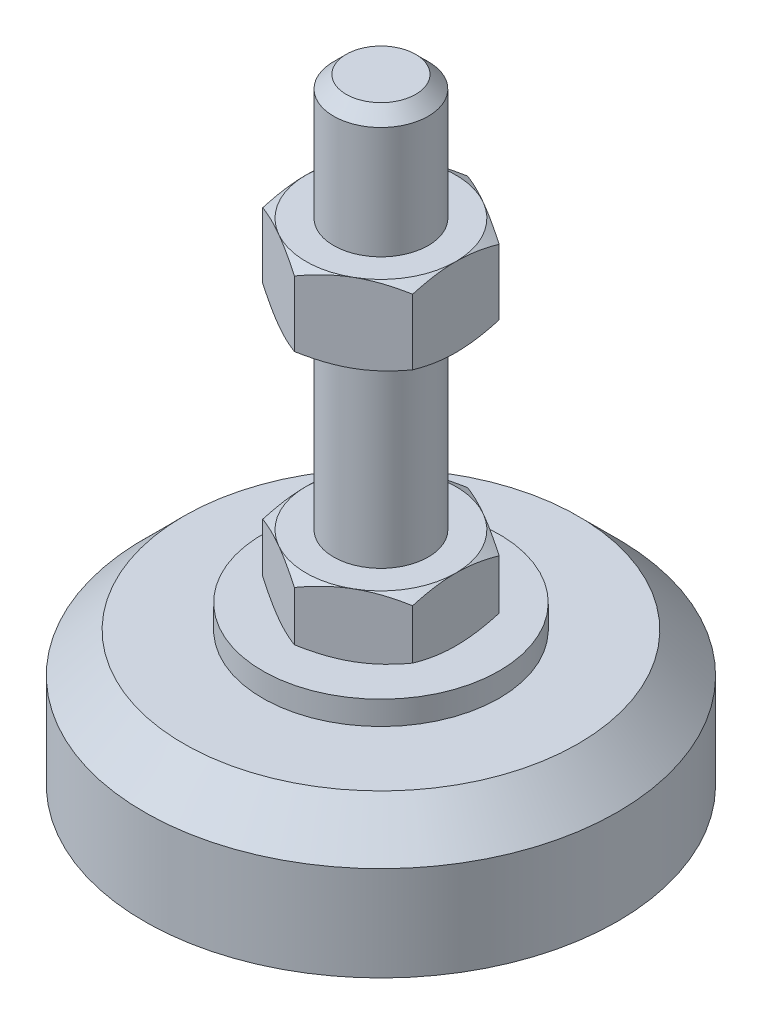
SolidWorks part; units mm, degrees
ref_plane "Спереди" through (0, 0, 0) normal (0, 0, 1) x (1, 0, 0)
ref_plane "Сверху" through (0, 0, 0) normal (0, 1, 0) x (1, 0, 0)
ref_plane "Справа" through (0, 0, 0) normal (1, 0, 0) x (0, 0, -1)
sketch "Эскиз1" plane through (0, 0, 0) normal (0, 0, 1) x (1, 0, 0)
  line L0 (0, 0) -> (-30, 0)
  line L3 (-30, 0) -> (-30, 12)
  line L5 (-15, 20) -> (-6, 20)
  line L12 (-6, 28) -> (-6, 76.4)
  line L13 (-6, 76.4) -> (-4.4, 78)
  line L14 (-4.4, 78) -> (0, 78)
  line L15 (0, 78) -> (0, 0) construction
  line L16 (-6, 20) -> (0, 20) construction
  line L17 (0, 0) -> (0, 78)
  line L18 (0, 0) -> (0, -7.9595) construction
  line L19 (-6, 28) -> (-6, 20)
  line L20 (-15, 20) -> (-15, 17)
  line L21 (-15, 17) -> (-25, 17)
  line L22 (-25, 17) -> (-30, 12)
  point P8 (-6, 52.2)
  point P23 (-10.5, 20)
  dimension "D1" = 12
  dimension "D2" = 20
  dimension "D3" = 8
  dimension "D4" = 60
  dimension "D5" = 6
  dimension "D6" = 1.6
  dimension "D7" = 45
  dimension "D8" = 30
  dimension "D10" = 50
  dimension "D11" = 12
  dimension "D12" = 45
  dimension "D13" = 3
revolve "Повернуть1" add sketch "Эскиз1" angle 360 about L17
sketch "Эскиз2" plane through (0, 20, 0) normal (0, 1, 0) x (1, 0, 0)
  line L1 (0, 10.9697) -> (-9.5, 5.4848)
  line L2 (-9.5, 5.4848) -> (-9.5, -5.4848)
  line L3 (-9.5, -5.4848) -> (0, -10.9697)
  line L4 (0, -10.9697) -> (9.5, -5.4848)
  line L5 (9.5, -5.4848) -> (9.5, 5.4848)
  line L6 (9.5, 5.4848) -> (0, 10.9697)
  circle A0 centre (0, 0) radius 9.5 construction
  dimension "D1" = 19
extrude "Бобышка-Вытянуть1" add sketch "Эскиз2" along normal up to vertex (8 mm away) up to point (-6, 28, 0)
ref_plane "Плоскость1" through (0, 52.2, 0) normal (0, 1, 0) x (1, 0, 0)
sketch "Эскиз3" plane through (0, 52.2, 0) normal (0, 1, 0) x (1, 0, 0)
  line L6 (9.5, 5.4848) -> (0, 10.9697)
  line L7 (0, 10.9697) -> (-9.5, 5.4848)
  line L8 (-9.5, 5.4848) -> (-9.5, -5.4848)
  line L9 (-9.5, -5.4848) -> (0, -10.9697)
  line L10 (0, -10.9697) -> (9.5, -5.4848)
  line L11 (9.5, -5.4848) -> (9.5, 5.4848)
  line L12 (9.5, 5.4848) -> (0, 10.9697)
  line L13 (0, 10.9697) -> (-9.5, 5.4848)
  line L14 (-9.5, 5.4848) -> (-9.5, -5.4848)
  line L15 (-9.5, -5.4848) -> (0, -10.9697)
  line L16 (0, -10.9697) -> (9.5, -5.4848)
  line L17 (9.5, -5.4848) -> (9.5, 5.4848)
  dimension "D1" = 0
extrude "Бобышка-Вытянуть2" add sketch "Эскиз3" along normal blind 10
sketch "Эскиз4" plane through (0, 0, 0) normal (0, 0, 1) x (1, 0, 0)
  line L0 (-9.5, 62.2) -> (-18.1603, 57.2)
  line L1 (-18.1603, 57.2) -> (-18.1603, 62.2)
  line L2 (-18.1603, 62.2) -> (-9.5, 62.2)
  line L3 (-18.1603, 57.2) -> (-9.5, 52.2)
  line L4 (50, 52.2) -> (-50, 52.2) construction
  line L5 (-9.5, 52.2) -> (-18.1603, 52.2)
  line L6 (-18.1603, 52.2) -> (-18.1603, 57.2)
  line L7 (-9.5, 62.2) -> (-9.5, 52.2) construction
  line L8 (-9.5, 28) -> (-16.4282, 28)
  line L9 (-16.4282, 28) -> (-16.4282, 24)
  line L10 (-16.4282, 24) -> (-9.5, 28)
  line L11 (-9.5, 20) -> (-16.4282, 24)
  line L12 (-16.4282, 24) -> (-16.4282, 20)
  line L13 (-16.4282, 20) -> (-9.5, 20)
  line L14 (0, 78) -> (0, 96.3793) construction
  dimension "D1" = 30
  dimension "D2" = 30
revolve "Вырез-Повернуть2" cut sketch "Эскиз4" angle 360 about L14
